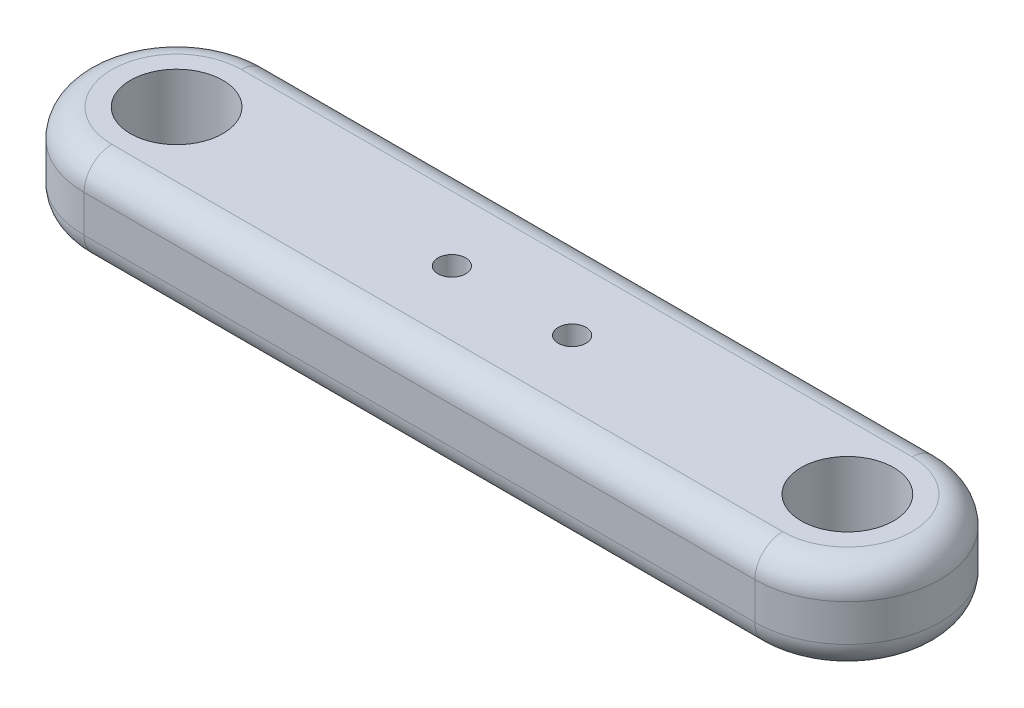
SolidWorks part; units mm, degrees
ref_plane "Front Plane" through (0, 0, 0) normal (0, 0, 1) x (1, 0, 0)
ref_plane "Top Plane" through (0, 0, 0) normal (0, 1, 0) x (1, 0, 0)
ref_plane "Right Plane" through (0, 0, 0) normal (1, 0, 0) x (0, 0, -1)
sketch "Sketch2" plane through (0, 0, 0) normal (0, 1, 0) x (1, 0, 0)
  line L4 (-36.25, 10) -> (36.25, 10)
  line L10 (36.25, -10) -> (-36.25, -10)
  arc A1 (0, -5) -> (0, 5) centre (0, 0) ccw
  circle A5 centre (0, 0) radius 5
  circle A6 centre (-36.25, 0) radius 5
  circle A7 centre (36.25, 0) radius 5
  arc A8 (-36.25, 10) -> (-36.25, -10) centre (-36.25, 0) ccw
  arc A9 (36.25, -10) -> (36.25, 10) centre (36.25, 0) ccw
  circle A10 centre (-36.25, 0) radius 10 construction
  circle A11 centre (36.25, 0) radius 10 construction
  point P3 (-19.375, 0)
  dimension "D1" = 5
  dimension "D2" = 5
extrude "Boss-Extrude1" add sketch "Sketch2" along normal blind 10 contours L10 A9 L4 A8 A5 A1 A6 A7
fillet "Fillet1" radius 3 8 edges at (-46.25, 0, 0) (0, 0, 10) (46.25, 0, 0) (-46.25, 10, 0) (0, 10, 10) (46.25, 10, 0) (0, 0, -10) (0, 10, -10)
sketch "Sketch3" plane through (0, 10, 0) normal (0, 1, 0) x (1, 0, 0)
  line L0 (0, 0) -> (-6.5, 0)
  line L1 (-6.5, 0) -> (7.6495, 0)
  circle A0 centre (0, 0) radius 5
  circle M5 centre (0, 0) radius 5
extrude "Boss-Extrude2" add sketch "Sketch3" against normal blind 10 contours L0 L1 M5 | L1 L0 M5
sketch "Sketch4" plane through (0, 10, 0) normal (0, 1, 0) x (1, 0, 0)
  circle A0 centre (-6.5, 0) radius 1.5
  circle A1 centre (6.5, 0) radius 1.5
extrude "Cut-Extrude1" cut sketch "Sketch4" against normal blind 14
